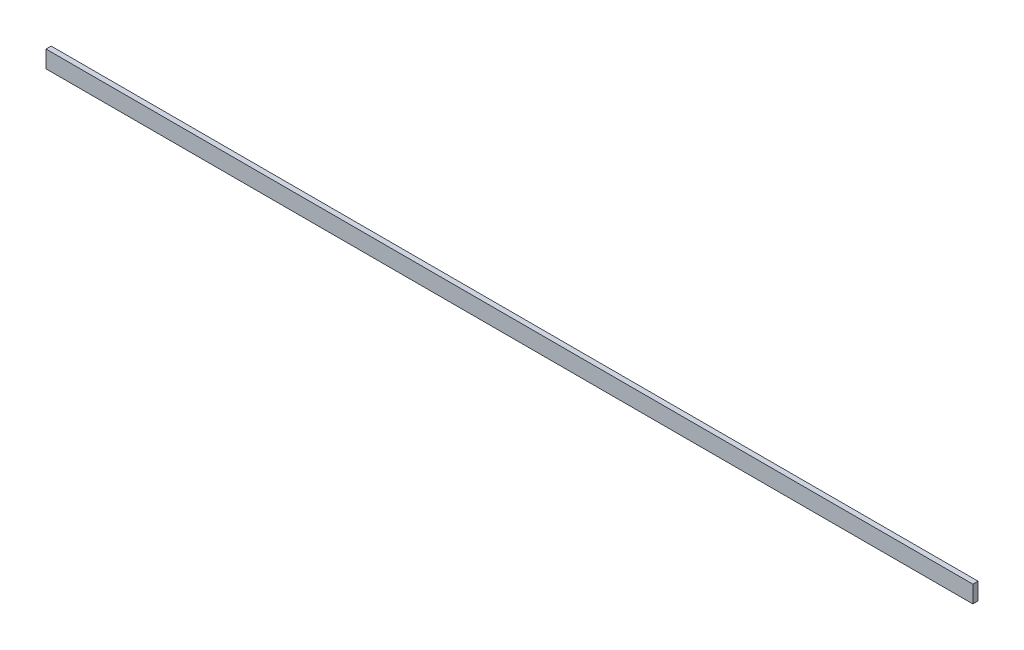
SolidWorks part; units mm, degrees
ref_plane "Front Plane" through (0, 0, 0) normal (0, 0, 1) x (1, 0, 0)
ref_plane "Top Plane" through (0, 0, 0) normal (0, 1, 0) x (1, 0, 0)
ref_plane "Right Plane" through (0, 0, 0) normal (1, 0, 0) x (0, 0, -1)
sketch "Sketch1" plane through (0, 0, 0) normal (0, 0, 1) x (1, 0, 0)
  line L1 (-270, 5) -> (270, 5)
  line L2 (-270, 5) -> (-270, -5)
  line L3 (-270, -5) -> (270, -5)
  line L4 (270, 5) -> (270, -5)
  line L5 (-270, 5) -> (270, -5) construction
  line L6 (-270, -5) -> (270, 5) construction
  point P0 (0, 0)
  dimension "D1" = 540
  dimension "D2" = 10
extrude "Boss-Extrude1" add sketch "Sketch1" along normal blind 3
